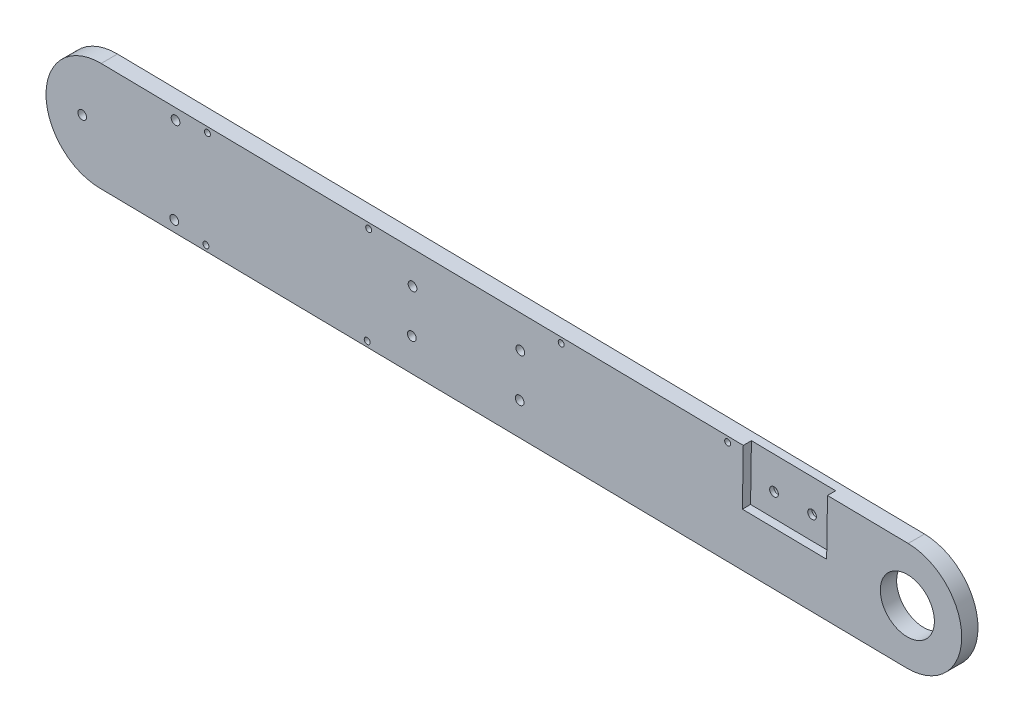
SolidWorks part; units mm, degrees
ref_plane "Front Plane" through (0, 0, 0) normal (0, 0, 1) x (1, 0, 0)
ref_plane "Top Plane" through (0, 0, 0) normal (0, 1, 0) x (1, 0, 0)
ref_plane "Right Plane" through (0, 0, 0) normal (1, 0, 0) x (0, 0, -1)
sketch "Sketch1" plane through (0, 0, 0) normal (0, 0, 1) x (1, 0, 0)
  line L0 (53.4525, 19.6302) -> (350.4185, 15.1383)
  line L1 (349.8135, -24.8571) -> (52.8475, -20.3652)
  arc A0 (350.4185, 15.1383) -> (349.8135, -24.8571) centre (350.116, -4.8594) cw
  arc A1 (52.8475, -20.3652) -> (53.4525, 19.6302) centre (53.15, -0.3675) cw
  arc A4 (53.4525, 19.6302) -> (52.8475, -20.3652) centre (53.15, -0.3675) ccw construction
  arc A5 (349.8135, -24.8571) -> (350.4185, 15.1383) centre (350.116, -4.8594) ccw construction
extrude "Boss-Extrude1" add sketch "Sketch1" along normal blind 6
sketch "Sketch2" plane through (0, 0, 0) normal (0, 0, -1) x (-1, 0, 0)
  circle A0 centre (-53.15, -0.3675) radius 12.45
  dimension "D1" = 24.9
extrude "Boss-Extrude2" add sketch "Sketch2" along normal offset from surface (5.25 mm away) 0.25
sketch "Sketch4" plane through (0, 0, 6) normal (0, 0, 1) x (1, 0, 0)
  line L0 (309.8752, -14.6486) -> (360.16, -15.4092)
  line L1 (360.16, -15.4092) -> (360.4744, 5.379)
  line L2 (360.4744, 5.379) -> (310.1896, 6.1396)
  line L3 (310.1896, 6.1396) -> (309.8752, -14.6486)
  line L4 (319.883, -14.2093) -> (320.1796, 5.3977) construction
  line L5 (359.577, -14.9003) -> (319.9722, -14.3013) construction
  line L6 (320.2715, 5.487) -> (359.8763, 4.8879) construction
  line L7 (359.9655, 4.796) -> (359.669, -14.8111) construction
  dimension "D1" = 10
  dimension "D2" = 0.5
  dimension "D3" = 0.5
  dimension "D4" = 0.5
extrude "Cut-Extrude1" [suppressed] cut sketch "Sketch4" against normal blind 3
sketch "Sketch5" plane through (0, 0, 6) normal (0, 0, 1) x (1, 0, 0)
  circle A0 centre (80.8294, 15.2156) radius 1.6
  circle A1 centre (46.4715, -0.2665) radius 1.6
  circle A2 centre (80.3455, -16.7764) radius 1.6
extrude "Cut-Extrude2" cut sketch "Sketch5" against normal up to next
sketch "Sketch6" plane through (0, 0, 0) normal (0, 0, -1) x (-1, 0, 0)
  circle A0 centre (-80.3455, -16.7764) radius 2.75
  circle A1 centre (-80.8294, 15.2156) radius 2.75
  dimension "D1" = 5.5
extrude "Cut-Extrude3" cut sketch "Sketch6" against normal blind 3.2
sketch "Sketch7" plane through (0, 0, -5.25) normal (0, 0, -1) x (-1, 0, 0)
  circle A0 centre (-46.4715, -0.2665) radius 2.75
  dimension "D1" = 5.5
extrude "Cut-Extrude4" cut sketch "Sketch7" against normal blind 3.2
sketch "Sketch8" plane through (0, 0, 0) normal (0, 0, -1) x (-1, 0, 0)
  line L0 (-119.2051, 13.6351) -> (-118.7514, -16.3615) construction
  line L1 (-118.9783, -1.3632) -> (-108.9783, -1.212) construction
  line L2 (-108.9783, 0.3879) -> (-121.0025, 0.206)
  line L3 (-350.4185, 15.1383) -> (-53.4525, 19.6302) construction
  line L4 (-108.9783, -2.8121) -> (-120.9541, -2.9933)
  line L5 (-118.7514, -16.3615) -> (-130.7514, -16.543) construction
  line L6 (-52.8475, -20.3652) -> (-349.8135, -24.8571) construction
  line L7 (-130.7401, -18.1428) -> (-118.7514, -18.0578)
  line L8 (-118.7742, -14.8578) -> (-130.7628, -14.9432)
  line L9 (-119.2051, 13.6351) -> (-131.2051, 13.4536) construction
  line L10 (-119.2051, 12.0351) -> (-131.1809, 11.8537)
  line L11 (-131.2293, 15.0534) -> (-119.2293, 15.2349)
  arc A0 (-119.2051, 12.0351) -> (-119.2293, 15.2349) centre (-119.2051, 13.6351) ccw
  arc A4 (-121.0025, 0.206) -> (-120.9541, -2.9933) centre (-120.9783, -1.3936) ccw
  arc A5 (-108.9783, -2.8121) -> (-108.9783, 0.3879) centre (-108.9783, -1.2121) ccw
  arc A6 (-130.7628, -14.9432) -> (-130.7401, -18.1428) centre (-130.7514, -16.543) ccw
  arc A7 (-118.7514, -18.0578) -> (-118.7742, -14.8578) centre (-118.7628, -16.4578) ccw
  arc A8 (-131.1809, 11.8537) -> (-131.2293, 15.0534) centre (-131.2051, 13.4536) cw
  dimension "D1" = 3.2
  dimension "D4" = 1.6
  dimension "D6" = 1.6
  dimension "D2" = 12
  dimension "D3" = 10
  dimension "D5" = 12
  dimension "D7" = 12
extrude "Cut-Extrude5" [suppressed] cut sketch "Sketch8" against normal up to next
sketch "Sketch9" [suppressed] plane through (0, 0, 0) normal (0, 0, -1) x (-1, 0, 0)
  arc A0 (-120.2172, -18.6289) -> (-120.2852, -14.1395) centre (-118.7514, -16.3615) ccw
  arc A1 (-120.671, 11.3676) -> (-120.7389, 15.8571) centre (-119.2051, 13.6351) ccw
  arc A2 (-120.2852, -14.1395) -> (-123.2849, -14.1849) centre (-121.7511, -16.4069) ccw
  arc A3 (-120.7389, 15.8571) -> (-123.7386, 15.8117) centre (-122.2048, 13.5897) ccw
  arc A4 (-123.2849, -14.1849) -> (-126.2845, -14.2303) centre (-124.7507, -16.4523) ccw
  arc A5 (-123.7386, 15.8117) -> (-126.7383, 15.7663) centre (-125.2044, 13.5442) ccw
  arc A6 (-126.2845, -14.2303) -> (-129.2842, -14.2757) centre (-127.7504, -16.4978) ccw
  arc A7 (-126.7383, 15.7663) -> (-129.7379, 15.7208) centre (-128.2041, 13.4988) ccw
  arc A8 (-129.2842, -14.2757) -> (-129.2162, -18.7652) centre (-130.75, -16.5432) ccw
  arc A9 (-129.7379, 15.7208) -> (-129.6699, 11.2314) centre (-131.2038, 13.4534) ccw
  arc A14 (-110.4441, -3.4796) -> (-110.5121, 1.0099) centre (-108.9783, -1.2121) ccw
  arc A15 (-110.5121, 1.0099) -> (-113.5117, 0.9645) centre (-111.9779, -1.2576) ccw
  arc A16 (-113.5117, 0.9645) -> (-116.5114, 0.9191) centre (-114.9776, -1.303) ccw
  arc A17 (-116.5114, 0.9191) -> (-119.5111, 0.8736) centre (-117.9772, -1.3484) ccw
  arc A18 (-119.5111, 0.8736) -> (-119.4431, -3.6158) centre (-120.9769, -1.3938) ccw
  arc A19 (-113.4438, -3.525) -> (-110.4441, -3.4796) centre (-111.9779, -1.2576) ccw
  arc A20 (-116.4434, -3.5704) -> (-113.4438, -3.525) centre (-114.9776, -1.303) ccw
  arc A21 (-119.4431, -3.6158) -> (-116.4434, -3.5704) centre (-117.9772, -1.3484) ccw
  arc A22 (-123.2169, -18.6744) -> (-120.2172, -18.6289) centre (-121.7511, -16.4069) ccw
  arc A23 (-126.2166, -18.7198) -> (-123.2169, -18.6744) centre (-124.7507, -16.4523) ccw
  arc A24 (-129.2162, -18.7652) -> (-126.2166, -18.7198) centre (-127.7504, -16.4978) ccw
  arc A25 (-123.6706, 11.3222) -> (-120.671, 11.3676) centre (-122.2048, 13.5897) ccw
  arc A26 (-126.6703, 11.2768) -> (-123.6706, 11.3222) centre (-125.2044, 13.5442) ccw
  arc A27 (-129.6699, 11.2314) -> (-126.6703, 11.2768) centre (-128.2041, 13.4988) ccw
  dimension "D1" = 5.4
  dimension "D2" = 5
extrude "Cut-Extrude6" [suppressed] cut sketch "Sketch9" against normal blind 3.2
sketch "Sketch10" plane through (0, 0, 0) normal (0, 0, -1) x (-1, 0, 0)
  circle A0 centre (-350.116, -4.8594) radius 9.95
  dimension "D1" = 19.9
extrude "Cut-Extrude7" cut sketch "Sketch10" against normal up to next
sketch "Sketch11" plane through (0, 0, 6) normal (0, 0, 1) x (1, 0, 0)
  circle A0 centre (207.6939, 5.2958) radius 1.6
  circle A1 centre (207.4519, -10.7024) radius 1.6
  circle A2 centre (168.0258, 5.8958) radius 1.6
  circle A3 centre (167.7838, -10.1024) radius 1.6
extrude "Cut-Extrude8" cut sketch "Sketch11" against normal up to next
sketch "Sketch12" plane through (0, 0, 0) normal (0, 0, -1) x (-1, 0, 0)
  circle A0 centre (-207.4519, -10.7024) radius 2.75
  circle A1 centre (-207.6939, 5.2958) radius 2.75
  circle A2 centre (-168.0258, 5.8958) radius 2.75
  circle A3 centre (-167.7838, -10.1024) radius 2.75
  dimension "D1" = 5.5
extrude "Cut-Extrude9" cut sketch "Sketch12" against normal blind 3
sketch "Sketch13" plane through (0, 0, 6) normal (0, 0, 1) x (1, 0, 0)
  line L0 (289.7325, 16.0563) -> (289.4225, -4.4414)
  line L1 (350.4185, 15.1383) -> (53.4525, 19.6302) construction
  line L2 (289.4225, -4.4414) -> (289.7325, 16.0563) construction
  line L3 (289.4225, -4.4414) -> (320.419, -4.9102)
  line L4 (320.419, -4.9102) -> (320.729, 15.5874)
  line L5 (320.729, 15.5874) -> (320.419, -4.9102) construction
  line L6 (320.729, 15.5874) -> (289.7325, 16.0563)
extrude "Cut-Extrude10" cut sketch "Sketch13" against normal blind 3
sketch "Sketch14" plane through (0, 0, 6) normal (0, 0, 1) x (1, 0, 0)
  circle A0 centre (312.0485, 3.7174) radius 1.6
  circle A1 centre (298.0501, 3.9291) radius 1.6
  dimension "D1" = 3.2
extrude "Cut-Extrude11" cut sketch "Sketch14" against normal up to next
sketch "Sketch15" plane through (0, 0, 0) normal (0, 0, -1) x (-1, 0, 0)
  circle A0 centre (-298.0501, 3.9291) radius 2.75
  circle A1 centre (-312.0485, 3.7174) radius 2.75
  dimension "D1" = 5.5
extrude "Cut-Extrude12" cut sketch "Sketch15" against normal blind 1.5
sketch "Sketch16" plane through (0, 0, 6) normal (0, 0, 1) x (1, 0, 0)
  circle A0 centre (92.5481, 17.0386) radius 1.1
  circle A1 centre (92.0036, -18.9573) radius 1.1
  circle A2 centre (151.9055, 16.1408) radius 1.1
  circle A3 centre (151.361, -19.8551) radius 1.1
  circle A4 centre (222.7444, 15.0693) radius 1.1
  circle A5 centre (283.9963, 14.1428) radius 1.1
extrude "Cut-Extrude13" cut sketch "Sketch16" against normal up to next
